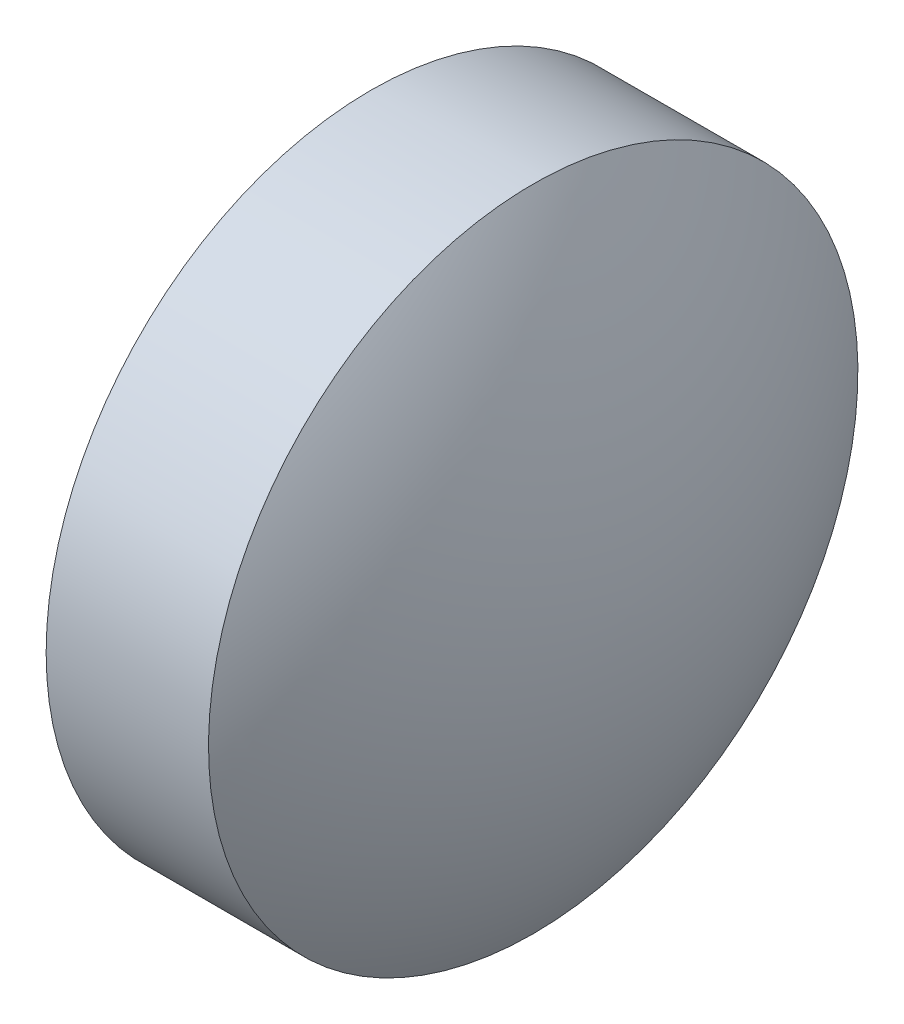
SolidWorks part; units mm, degrees
ref_plane "前视基准面" through (0, 0, 0) normal (0, 0, 1) x (1, 0, 0)
ref_plane "上视基准面" through (0, 0, 0) normal (0, 1, 0) x (1, 0, 0)
ref_plane "右视基准面" through (0, 0, 0) normal (1, 0, 0) x (0, 0, -1)
sketch "草图2" plane through (0, 0, 0) normal (0, 0, 1) x (1, 0, 0)
  line L0 (9.7117, 7.2421) -> (10.7117, 7.2421)
  line L1 (10.7117, 7.2421) -> (10.7446, 3.2421)
  line L2 (10.7446, 3.2421) -> (9.7117, 3.2421)
  line L3 (9.7117, 3.2421) -> (9.7117, 7.2421)
  line L4 (9.1399, 5.2421) -> (11.2999, 5.2421) construction
  arc A0 (9.7117, 7.2421) -> (9.7117, 3.2421) centre (12.9239, 5.2421) ccw
  arc A1 (10.7446, 3.2421) -> (10.7117, 7.2421) centre (7.516, 5.2156) ccw
  dimension "D1" = 1
  dimension "D2" = 4
  dimension "D3" = 2.16
revolve "旋转1" add sketch "草图2" angle 360 about L4
